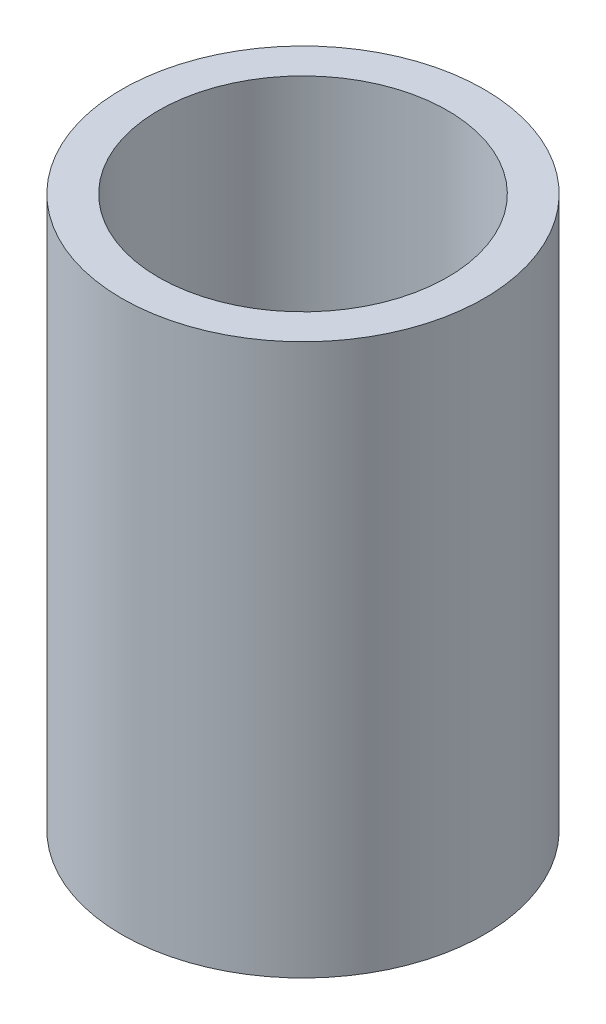
SolidWorks part; units mm, degrees
material "PVC Rigid"
ref_plane "Front" through (0, 0, 0) normal (0, 0, 1) x (1, 0, 0)
ref_plane "Top" through (0, 0, 0) normal (0, 1, 0) x (1, 0, 0)
ref_plane "Right" through (0, 0, 0) normal (1, 0, 0) x (0, 0, -1)
sketch "Sketch1" plane through (0, 0, 0) normal (0, 1, 0) x (1, 0, 0)
  circle A0 centre (0, 0) radius 16.7005
  circle A1 centre (0, 0) radius 13.3223
  dimension "D1" = 26.6446
  dimension "D2" = 33.401
extrude "Boss-Extrude1" add sketch "Sketch1" along normal blind 50.8
